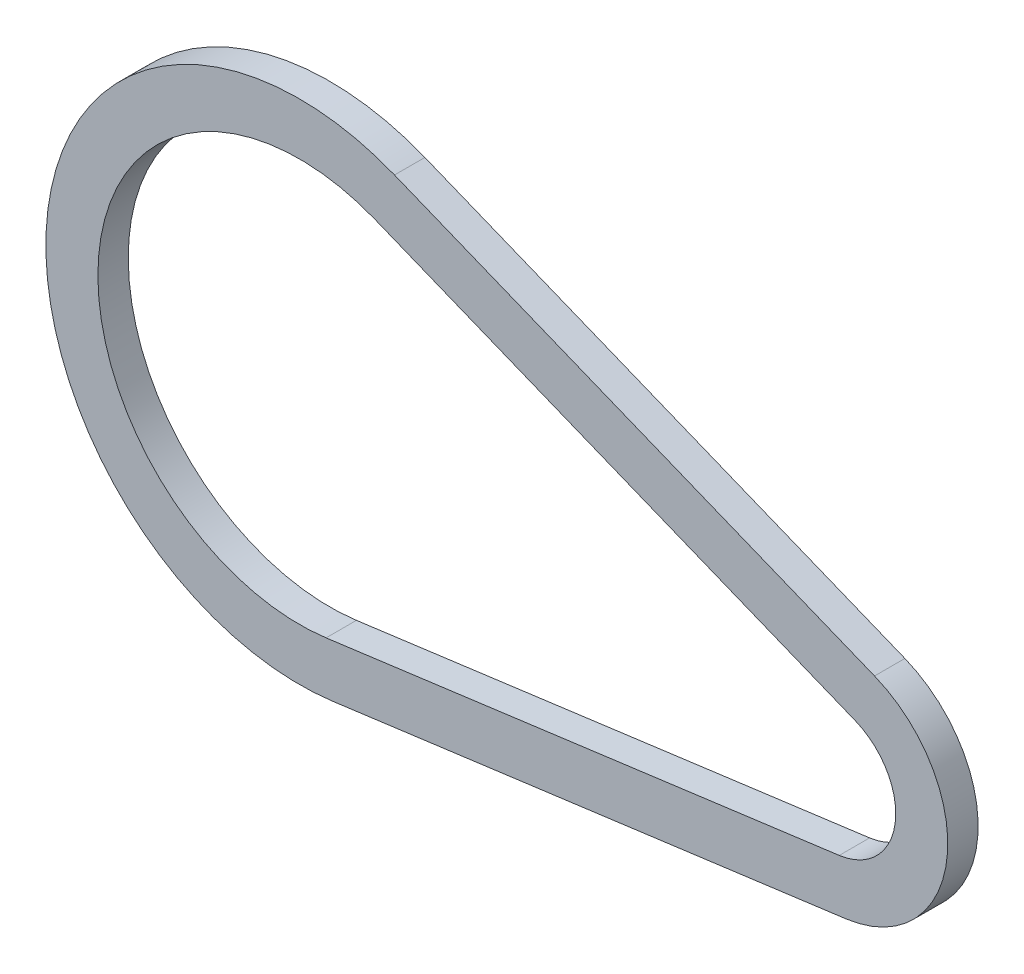
SolidWorks part; units mm, degrees
ref_plane "Front Plane" through (0, 0, 0) normal (0, 0, 1) x (1, 0, 0)
ref_plane "Top Plane" through (0, 0, 0) normal (0, 1, 0) x (1, 0, 0)
ref_plane "Right Plane" through (0, 0, 0) normal (1, 0, 0) x (0, 0, -1)
sketch "Sketch1" plane through (0, 0, 0) normal (0, 0, 1) x (1, 0, 0)
  line L0 (-105.0873, 58.6167) -> (5.617, 13.9086)
  line L1 (-116.3753, -30.5949) -> (1.9757, -14.8693)
  line L2 (-100.5937, 69.7436) -> (10.1106, 25.0355)
  line L3 (-114.7947, -42.4903) -> (3.5563, -26.7648)
  arc A0 (1.9757, -14.8693) -> (5.617, 13.9086) centre (0, 0) ccw
  arc A1 (-105.0873, 58.6167) -> (-116.3753, -30.5949) centre (-122.5, 15.5) ccw
  arc A2 (3.5563, -26.7648) -> (10.1106, 25.0355) centre (0, 0) ccw
  arc A3 (-100.5937, 69.7436) -> (-114.7947, -42.4903) centre (-122.5, 15.5) ccw
  point P1 (-120.5053, 22.0166)
  point P4 (0, 0)
  point P9 (0, 0)
  dimension "D1" = 93
  dimension "D2" = 30
  dimension "D3" = 122.5
  dimension "D4" = 15.5
  dimension "D5" = 12
extrude "Boss-Extrude1" add sketch "Sketch1" along normal mid plane 7
